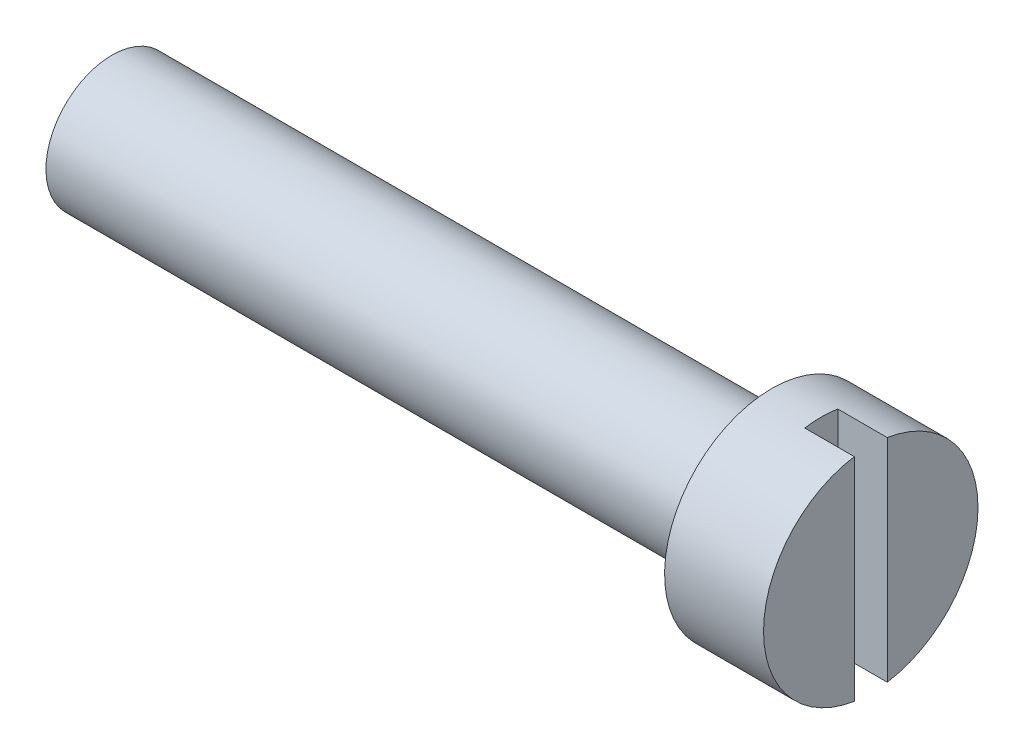
SolidWorks part; units mm, degrees
material "AISI 316 Stainless Steel Sheet (SS)"
ref_plane "Front Plane" through (0, 0, 0) normal (0, 0, 1) x (1, 0, 0)
ref_plane "Top Plane" through (0, 0, 0) normal (0, 1, 0) x (1, 0, 0)
ref_plane "Right Plane" through (0, 0, 0) normal (1, 0, 0) x (0, 0, -1)
sketch "Sketch1" plane through (0, 0, 0) normal (0, 0, 1) x (1, 0, 0)
  line L0 (0, 0) -> (-23, 0)
  line L1 (-23, 0) -> (-23, 2)
  line L2 (-23, 2) -> (-3, 2)
  line L3 (-3, 2) -> (-3, 3.25)
  line L4 (-3, 3.25) -> (0, 3.25)
  line L5 (0, 3.25) -> (0, 0)
  dimension "D1" = 3
  dimension "D2" = 20
  dimension "D3" = 2
  dimension "D4" = 3.25
revolve "Revolve1" add sketch "Sketch1" angle 360 about L0
sketch "Sketch2" plane through (0, 0, 0) normal (1, 0, 0) x (0, 0, -1)
  line L1 (-0.5, -3.25) -> (0.5, -3.25)
  line L2 (-0.5, -3.25) -> (-0.5, 3.25)
  line L3 (-0.5, 3.25) -> (0.5, 3.25)
  line L4 (0.5, -3.25) -> (0.5, 3.25)
  line L5 (-0.5, -3.25) -> (0.5, 3.25) construction
  line L6 (-0.5, 3.25) -> (0.5, -3.25) construction
  circle A0 centre (0, 0) radius 3.25 construction
  point P0 (0, 0)
  dimension "D1" = 1
extrude "Cut-Extrude1" cut sketch "Sketch2" against normal blind 1.5
